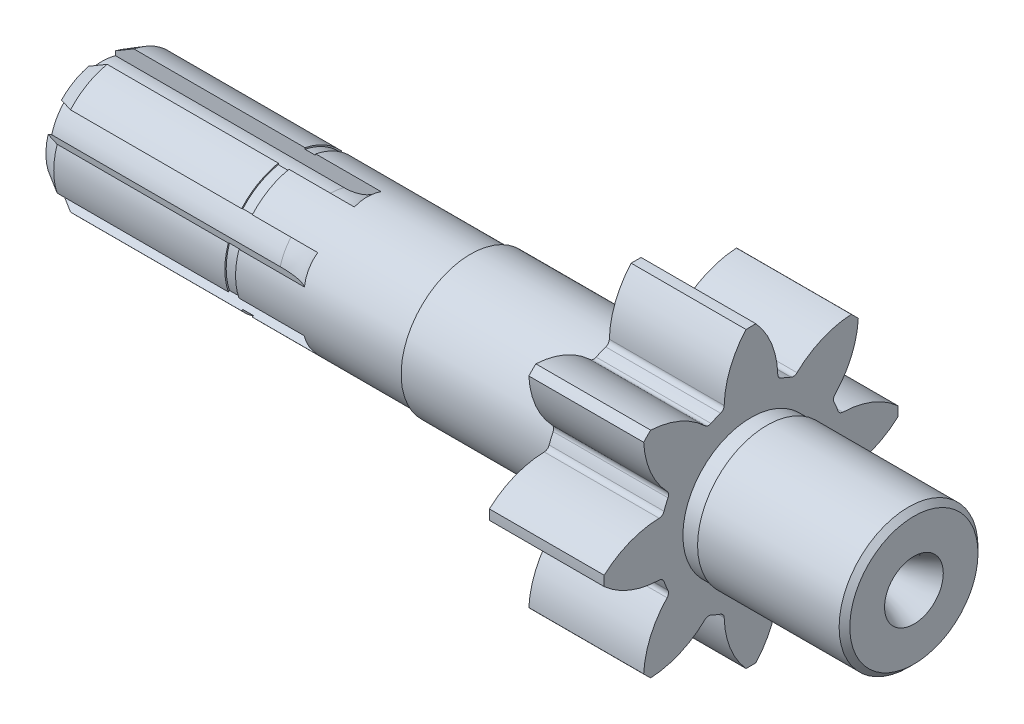
SolidWorks part; units mm, degrees
material " 40Х ГОСТ 4543-71"
ref_plane "Спереди" through (0, 0, 0) normal (0, 0, 1) x (1, 0, 0)
ref_plane "Сверху" through (0, 0, 0) normal (0, 1, 0) x (1, 0, 0)
ref_plane "Справа" through (0, 0, 0) normal (1, 0, 0) x (0, 0, -1)
sketch "Эскиз1" plane through (0, 0, 0) normal (1, 0, 0) x (0, 0, -1)
  circle A0 centre (0, 0) radius 12.5
  dimension "D1" = 25
extrude "Бобышка-Вытянуть1" add sketch "Эскиз1" along normal blind 50
sketch "Эскиз3" plane through (50, 0, 0) normal (1, 0, 0) x (0, 0, -1)
  circle A0 centre (0, 0) radius 12.5
  dimension "D1" = 25
extrude "Бобышка-Вытянуть2" add sketch "Эскиз3" along normal blind 19
sketch "Эскиз4" plane through (69, 0, 0) normal (1, 0, 0) x (0, 0, -1)
  circle A0 centre (0, 0) radius 13
  dimension "D1" = 26
extrude "Бобышка-Вытянуть3" add sketch "Эскиз4" along normal blind 31
sketch "Эскиз5" plane through (100, 0, 0) normal (1, 0, 0) x (0, 0, -1)
  circle A0 centre (0, 0) radius 17.25
  dimension "D1" = 34.5
extrude "Бобышка-Вытянуть4" add sketch "Эскиз5" along normal blind 21.5
sketch "Эскиз6" plane through (121.5, 0, 0) normal (1, 0, 0) x (0, 0, -1)
  circle A0 centre (0, 0) radius 13
  dimension "D1" = 26
extrude "Бобышка-Вытянуть5" add sketch "Эскиз6" along normal blind 30.5
sketch "Эскиз7" plane through (0, 0, 0) normal (-1, 0, 0) x (0, 0, 1)
  line L0 (2.5, 12.2474) -> (2.5, 9.424)
  line L1 (-2.5, 12.2474) -> (-2.5, 9.424)
  line L2 (0, 0) -> (0, 17.25) construction
  arc A0 (2.5, 9.424) -> (-2.5, 9.424) centre (0, 0) ccw
  arc A1 (2.5, 12.2474) -> (-2.5, 12.2474) centre (0, 0) ccw
  circle A2 centre (0, 0) radius 17.25 construction
  dimension "D1" = 19.5
  dimension "D2" = 25
  dimension "D3" = 5
sketch "Эскиз8" plane through (0, 0, 0) normal (0, 0, 1) x (1, 0, 0)
  line L0 (0, 9.422) -> (42.7829, 9.422)
  line L1 (0, 12.2474) -> (0, 9.424) construction
  line L2 (0, 12.2474) -> (0, 9.424) construction
  line L3 (69, 12.5) -> (0, 12.5) construction
  arc A0 (42.7829, 9.422) -> (50, 12.5) centre (42.7829, 19.422) ccw
  dimension "D1" = 10
  dimension "D2" = 9.422
  dimension "D3" = 50
sweep "Вырез-По траектории1" cut profiles "Эскиз7" path "Эскиз8"
pattern_circular "Круговой массив1" count 6 over 360 about axis through (0, 0, 0) along (1, 0, 0) of "Вырез-По траектории1"
hole_wizard "Отверстие1" positions "Эскиз10" profile "Эскиз9" legacy
sketch "Эскиз10" plane through (152, 0, 0) normal (1, 0, 0) x (0, 0, -1)
  point P0 (0, 0)
sketch "Эскиз9" plane through (152, 0, 0) normal (0, 1, 0) x (0, 0, -1)
  line L0 (0, 0) -> (0, 10.5)
  line L1 (0, 10.5) -> (0.5, 10.5)
  line L2 (0.5, 10.5) -> (5.5, 0)
  line L3 (5.5, 0) -> (0, 0)
  line L4 (0, 110) -> (0, -10) construction
  dimension "Внутренний диаметр" = 1
  dimension "Глубина" = 10.5
  dimension "Наружный диаметр" = 11
hole_wizard "Отверстие2" positions "Эскиз13" profile "Эскиз14" legacy
sketch "Эскиз13" plane through (0, 0, 0) normal (-1, 0, 0) x (0, 0, 1)
  point P0 (0, 0)
sketch "Эскиз14" plane through (0, 0, 0) normal (0, 1, 0) x (0, 0, 1)
  line L0 (0, 0) -> (0, 11.3004)
  line L1 (0, 11.3004) -> (0.5, 11)
  line L2 (0.5, 11) -> (5.25, 0)
  line L3 (5.25, 0) -> (0, 0)
  line L4 (0, -9.9017) -> (0, 117.2029) construction
  line L5 (0, 11.3004) -> (-0.5, 11) construction
  dimension "Внутренний Диаметр" = 1
  dimension "Глубина" = 11
  dimension "Наружный диаметр" = 10.5
  dimension "Угол заточки сверла" = 118
sketch "Эскиз15" plane through (0, 0, 0) normal (0, 1, 0) x (1, 0, 0)
  line L0 (0, 0) -> (37.5, 0) construction
  line L1 (35.5, 15.25) -> (37.5, 15.25)
  line L2 (35.5, 15.25) -> (35.5, 12.25)
  line L3 (35.5, 12.25) -> (37.5, 12.25)
  line L4 (37.5, 15.25) -> (37.5, 12.25)
  dimension "D1" = 35.5
  dimension "D2" = 2
  dimension "D3" = 12.25
  dimension "D4" = 3
revolve "Вырез-Повернуть1" cut sketch "Эскиз15" angle 360 about L0
chamfer "Фаска1" distance 2 angle 60 6 edges at (0, 10.8253, -6.25) (0, 0, -12.5) (0, -10.8253, -6.25) (0, -10.8253, 6.25) (0, 0, 12.5) (0, 10.8253, 6.25)
chamfer "Фаска2" distance 1 angle 45 1 edges at (152, 0, -13)
sketch "Эскиз16" plane through (100, 0, 0) normal (-1, 0, 0) x (0, 0, 1)
  line L0 (0, 0) -> (0, 27.5) construction
  line L1 (0, 0) -> (5.365, 26.9716) construction
  line L2 (0, 0) -> (-5.365, 26.9716) construction
  arc A0 (5.0214, 16.503) -> (-5.0214, 16.503) centre (0, 0) ccw
  circle A1 centre (0, 0) radius 17.25 construction
  circle A2 centre (0, 0) radius 22 construction
  arc A3 (5.365, 26.9716) -> (-5.365, 26.9716) centre (0, 0) ccw
  arc A4 (-0.9277, 27.4843) -> (-5.0214, 16.503) centre (10.976, 16.7931) ccw
  arc A5 (5.0214, 16.503) -> (0.9277, 27.4843) centre (-10.976, 16.7931) ccw
  point P7 (4.292, 21.5773)
  point P11 (-4.292, 21.5773)
  circle M1 centre (0, 0) radius 17.25
  dimension "D1" = 44
  dimension "D2" = 55
  dimension "D4" = 32
  dimension "D3" = 11.25
extrude "Бобышка-Вытянуть6" add sketch "Эскиз16" against normal up to surface (21.5 mm away) contours A5 A3 A4 M1 up to face at (121.5, 0, -17.25)
fillet "Скругление1" radius 1 2 edges at (110.75, 16.503, -5.0214) (110.75, 16.503, 5.0214)
pattern_circular "Круговой массив2" count 8 over 360 about axis through (0, 0, 0) along (1, 0, 0) of "Бобышка-Вытянуть6", "Скругление1"
sketch "Эскиз18" plane through (0, 0, 0) normal (0, 0, 1) x (1, 0, 0)
  line L0 (0, 0) -> (145.5628, 0) construction
  line L1 (100, 13) -> (100, -13) construction
  line L2 (97, 15.75) -> (100, 15.75)
  line L3 (97, 15.75) -> (97, 12.75)
  line L4 (97, 12.75) -> (100, 12.75)
  line L5 (100, 15.75) -> (100, 12.75)
  line L6 (121.5, -13) -> (121.5, 13) construction
  line L7 (124.5, 12.75) -> (121.5, 12.75)
  line L8 (124.5, 12.75) -> (124.5, 15.75)
  line L9 (124.5, 15.75) -> (121.5, 15.75)
  line L10 (121.5, 12.75) -> (121.5, 15.75)
  dimension "D1" = 25.5
  dimension "D2" = 3
  dimension "D3" = 3
revolve "Вырез-Повернуть2" cut sketch "Эскиз18" angle 360 about L0
